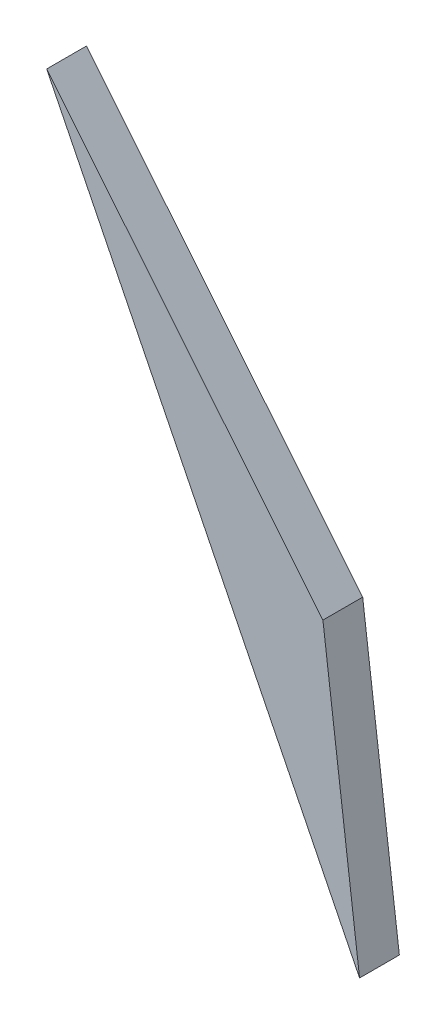
SolidWorks part; units mm, degrees
ref_plane "Plan de face" through (0, 0, 0) normal (0, 0, 1) x (1, 0, 0)
ref_plane "Plan de dessus" through (0, 0, 0) normal (0, 1, 0) x (1, 0, 0)
ref_plane "Plan de droite" through (0, 0, 0) normal (1, 0, 0) x (0, 0, -1)
sketch "Esquisse1" plane through (0, 0, 0) normal (0, 0, 1) x (1, 0, 0)
  line L0 (-0.104, -23.2277) -> (-2.8693, -1.2277)
  line L1 (-2.8693, -1.2277) -> (-23.7103, 24.3585)
  line L2 (-23.7103, 24.3585) -> (-0.104, -23.2277)
  line L3 (-64.2396, 74.1157) -> (-2.326, -1.8946) construction
  line L4 (5.5403, -68.1325) -> (-2.9766, -0.3741) construction
  dimension "D1" = 33
  dimension "D2" = 22
extrude "Boss.-Extru.1" add sketch "Esquisse1" along normal blind 3
